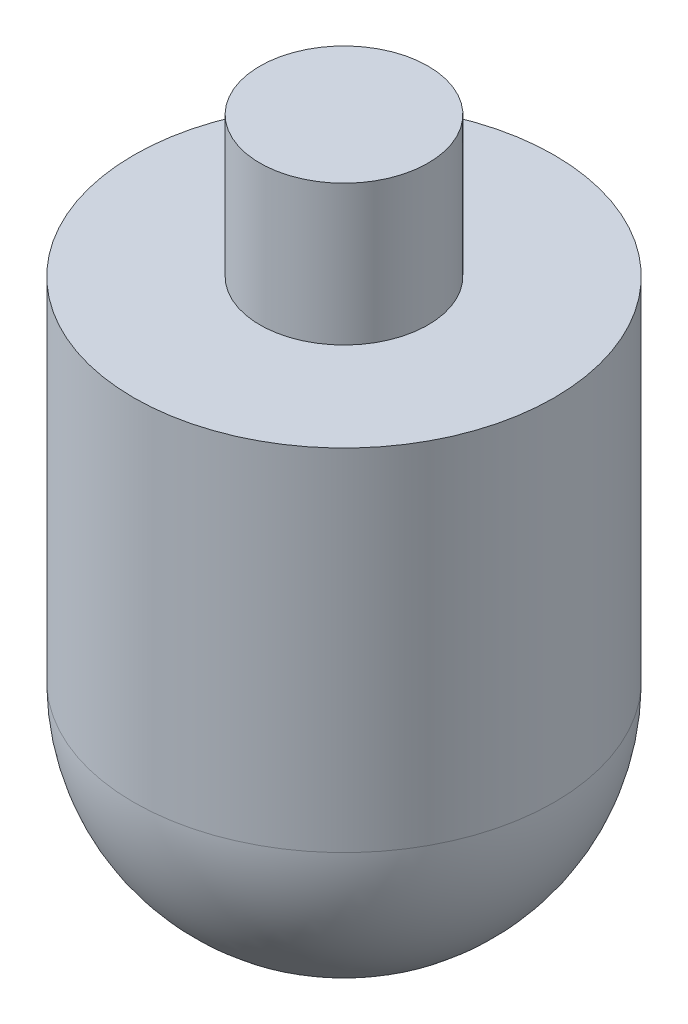
SolidWorks part; units mm, degrees
ref_plane "Front Plane" through (0, 0, 0) normal (0, 0, 1) x (1, 0, 0)
ref_plane "Top Plane" through (0, 0, 0) normal (0, 1, 0) x (1, 0, 0)
ref_plane "Right Plane" through (0, 0, 0) normal (1, 0, 0) x (0, 0, -1)
sketch "Sketch1" plane through (0, 0, 0) normal (0, 0, 1) x (1, 0, 0)
  line L1 (0, 0) -> (0, 101.2972) construction
  line L3 (0, 35) -> (6, 35)
  line L4 (6, 35) -> (6, 25)
  line L5 (6, 25) -> (15, 25)
  line L6 (15, 25) -> (15, 0)
  line L8 (0, 35) -> (0, -15)
  arc A0 (0, -15) -> (15, 0) centre (0, 0) ccw
  dimension "D1" = 15
  dimension "D2" = 12
  dimension "D3" = 30
  dimension "D4" = 10
  dimension "D5" = 25
revolve "Revolve1" add sketch "Sketch1" angle 360 about L1
